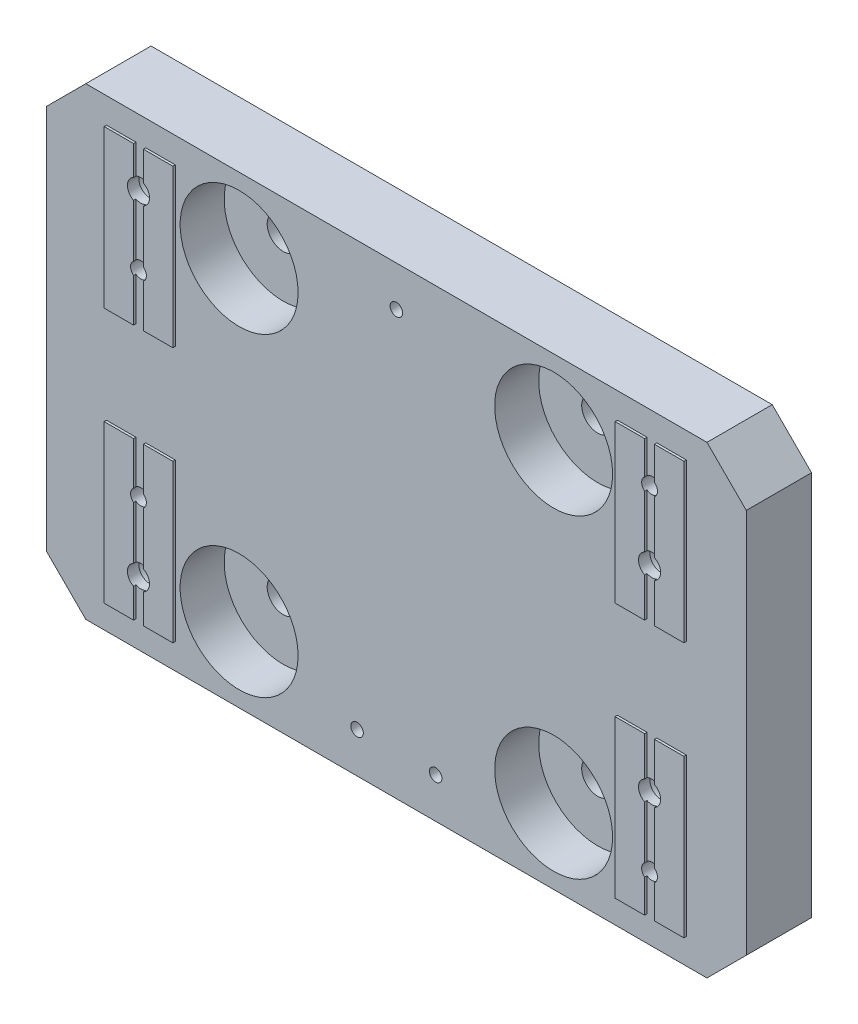
SolidWorks part; units mm, degrees
material "AISI 304"
ref_plane "Front" through (0, 0, 0) normal (0, 0, 1) x (1, 0, 0)
ref_plane "Top" through (0, 0, 0) normal (0, 1, 0) x (1, 0, 0)
ref_plane "Right" through (0, 0, 0) normal (1, 0, 0) x (0, 0, -1)
sketch "Sketch3" plane through (0, 0, 0) normal (0, 0, 1) x (1, 0, 0)
  line L1 (0, 0) -> (226.06, 0)
  line L2 (0, 0) -> (0, -149.86)
  line L3 (0, -149.86) -> (226.06, -149.86)
  line L4 (226.06, 0) -> (226.06, -149.86)
  dimension "D1" = 226.06
  dimension "D2" = 149.86
extrude "Extrude2" add sketch "Sketch3" along normal blind 21.844
sketch "Sketch4" plane through (0, 0, 21.844) normal (0, 0, 1) x (1, 0, 0)
  line L0 (0, -74.93) -> (226.06, -74.93) construction
  line L1 (0, 0) -> (0, -149.86) construction
  line L2 (226.06, -149.86) -> (226.06, 0) construction
  line L3 (113.03, 0) -> (113.03, -149.86) construction
  line L4 (226.06, 0) -> (0, 0) construction
  line L5 (0, -149.86) -> (226.06, -149.86) construction
  line L6 (41.6052, -141.605) -> (19.3802, -141.605)
  line L7 (41.6052, -8.255) -> (41.6052, -59.055)
  line L8 (19.3802, -8.255) -> (19.3802, -59.055)
  line L9 (41.6052, -90.805) -> (19.3802, -90.805)
  line L10 (41.6052, -141.605) -> (41.6052, -90.805)
  line L11 (19.3802, -141.605) -> (19.3802, -90.805)
  line L12 (41.6052, -59.055) -> (19.3802, -59.055)
  line L13 (184.4548, -141.605) -> (184.4548, -90.805)
  line L14 (206.6798, -141.605) -> (206.6798, -90.805)
  line L15 (41.6052, -8.255) -> (19.3802, -8.255)
  line L16 (184.4548, -8.255) -> (184.4548, -59.055)
  line L17 (206.6798, -8.255) -> (206.6798, -59.055)
  line L18 (206.6798, -141.605) -> (184.4548, -141.605)
  line L19 (0, 0) -> (226.06, 0)
  line L20 (0, 0) -> (0, -149.86)
  line L21 (0, -149.86) -> (226.06, -149.86)
  line L22 (226.06, 0) -> (226.06, -149.86)
  line L23 (206.6798, -90.805) -> (184.4548, -90.805)
  line L24 (206.6798, -59.055) -> (184.4548, -59.055)
  line L25 (206.6798, -8.255) -> (184.4548, -8.255)
  dimension "D5" = 15.875
  dimension "D6" = 15.875
  dimension "D7" = 50.8
  dimension "D8" = 50.8
  dimension "D9" = 71.4248
  dimension "D10" = 71.4248
  dimension "D12" = 22.225
extrude "Extrude4" cut sketch "Sketch4" against normal blind 0.762
hole_wizard "1/4-20 Tapped Hole1" positions "Sketch13" profile "Sketch12" tap size "1/4-20" standard "Ansi Inch" end condition through all
sketch "Sketch13" plane through (0, 0, 0) normal (0, 0, -1) x (-1, 0, 0)
  line L0 (-226.06, -74.93) -> (0, -74.93) construction
  line L1 (-226.06, -149.86) -> (-226.06, 0) construction
  line L2 (0, 0) -> (0, -149.86) construction
  line L4 (-113.03, 0) -> (-113.03, -149.86) construction
  line L5 (-226.06, 0) -> (0, 0) construction
  line L6 (0, -149.86) -> (-226.06, -149.86) construction
  line L11 (-195.58, -20.955) -> (-195.58, -74.93) construction
  line L13 (-195.58, -74.93) -> (-195.58, -128.905) construction
  line L15 (-30.48, -43.18) -> (-30.48, -74.93) construction
  line L17 (-30.48, -74.93) -> (-30.48, -106.68) construction
  point P3 (-195.58, -20.955)
  point P5 (-195.58, -128.905)
  point P7 (-30.48, -43.18)
  point P9 (-30.48, -106.68)
  dimension "D1" = 82.55
  dimension "D2" = 82.55
  dimension "D3" = 107.95
  dimension "D4" = 63.5
sketch "Sketch12" plane through (195.58, -20.955, 0) normal (1, 0, 0) x (0, 1, 0)
  line L0 (0, 0) -> (0, 21.844)
  line L1 (0, 21.844) -> (2.5527, 21.844)
  line L2 (2.5527, 21.844) -> (2.5527, 0)
  line L5 (2.5527, 0) -> (0, 0)
  line L11 (0, -6.35) -> (0, 107.95) construction
  dimension "Thru Tap Drill Dia." = 5.1054
  dimension "Thru Tap Drill Depth" = 21.844
cosmetic thread "Hole Thread5" parameters "D2"=6.35
cosmetic thread "Hole Thread6" parameters "D2"=6.35
cosmetic thread "Hole Thread7" parameters "D2"=6.35
cosmetic thread "Hole Thread8" parameters "D2"=6.35
hole_wizard "CBORE for 3/8 Socket Head Cap Screw1" positions "Sketch16" profile "Sketch15" counterbore size "3/8" standard "Ansi Inch" end condition through all
sketch "Sketch16" plane through (0, 0, 21.082) normal (0, 0, 1) x (1, 0, 0)
  line L0 (163.83, -125.73) -> (62.23, -125.73) construction
  line L1 (163.83, -24.13) -> (163.83, -125.73) construction
  line L2 (163.83, -24.13) -> (62.23, -24.13) construction
  line L3 (62.23, -125.73) -> (62.23, -24.13) construction
  line L4 (226.06, -74.93) -> (163.83, -74.93) construction
  line L5 (226.06, -149.86) -> (226.06, 0) construction
  line L6 (113.03, -149.86) -> (113.03, -125.73) construction
  line L7 (0, -149.86) -> (226.06, -149.86) construction
  point P0 (62.23, -125.73)
  point P1 (163.83, -24.13)
  point P4 (62.23, -24.13)
  point P7 (163.83, -125.73)
  dimension "D1" = 101.6
  dimension "D2" = 101.6
sketch "Sketch15" plane through (62.23, -125.73, 21.082) normal (1, 0, 0) x (0, -1, 0)
  line L0 (0, 0) -> (0, 21.082)
  line L1 (0, 21.082) -> (5.1587, 21.082)
  line L3 (5.1587, 21.082) -> (5.1587, 14.224)
  line L4 (5.1587, 14.224) -> (19.05, 14.224)
  line L5 (19.05, 14.224) -> (19.05, 0)
  line L7 (19.05, 0) -> (0, 0)
  line L11 (0, -6.35) -> (0, 107.95) construction
  dimension "Thru Hole Dia." = 10.3175
  dimension "Thru Hole Depth" = 21.082
  dimension "C'Bore Dia." = 38.1
  dimension "C'Bore Depth" = 14.224
sketch "Sketch17" plane through (0, 0, 21.844) normal (0, 0, 1) x (1, 0, 0)
  line L0 (195.58, -128.905) -> (195.58, -141.605) construction
  line L1 (197.1675, -141.605) -> (193.9925, -141.605)
  line L2 (197.1675, -141.605) -> (197.1675, -8.255)
  line L3 (197.1675, -8.255) -> (193.9925, -8.255)
  line L4 (193.9925, -141.605) -> (193.9925, -8.255)
  line L5 (32.0675, -141.605) -> (28.8925, -141.605)
  line L6 (32.0675, -141.605) -> (32.0675, -8.255)
  line L7 (32.0675, -8.255) -> (28.8925, -8.255)
  line L8 (28.8925, -141.605) -> (28.8925, -8.255)
  line L9 (30.48, -106.68) -> (30.48, -141.605) construction
  line L10 (184.4548, -141.605) -> (206.6798, -141.605) construction
  line L11 (206.6798, -8.255) -> (184.4548, -8.255) construction
  line L12 (19.3802, -141.605) -> (41.6052, -141.605) construction
  line L13 (41.6052, -8.255) -> (19.3802, -8.255) construction
  dimension "D1" = 3.175
extrude "Cut-Extrude1" cut sketch "Sketch17" against normal up to surface (0.762 mm away) up to face at (81.28, -125.73, 21.082)
hole_wizard "CBORE for 1/4 Socket Head Cap Screw1" positions "Sketch20" profile "Sketch19" counterbore size "1/4" standard "Ansi Inch" end condition through all
sketch "Sketch20" plane through (0, 0, 0) normal (0, 0, -1) x (-1, 0, 0)
  line L0 (-30.48, -128.905) -> (-30.48, -20.955) construction
  line L1 (-195.58, -43.18) -> (-195.58, -106.68) construction
  line L2 (-195.58, -43.18) -> (-30.48, -43.18) construction
  line L3 (-195.58, -43.18) -> (-195.58, -20.955) construction
  line L4 (-30.48, -106.68) -> (-195.58, -106.68) construction
  line L5 (-195.58, -20.955) -> (-30.48, -20.955) construction
  line L6 (-195.58, -128.905) -> (-30.48, -128.905) construction
  line L7 (-30.48, -106.68) -> (-30.48, -128.905) construction
  point P0 (-195.58, -106.68)
  point P1 (-195.58, -43.18)
  point P3 (-30.48, -20.955)
  point P5 (-30.48, -128.905)
sketch "Sketch19" plane through (195.58, -106.68, 0) normal (1, 0, 0) x (0, 1, 0)
  line L0 (0, 0) -> (0, 21.844)
  line L1 (0, 21.844) -> (3.5712, 21.844)
  line L3 (3.5712, 21.844) -> (3.5712, 18.161)
  line L4 (5.5562, 18.161) -> (3.5712, 18.161)
  line L5 (5.5562, 18.161) -> (5.5562, 0.635)
  line L6 (5.5562, 0.635) -> (6.1913, 0)
  line L7 (6.1913, 0) -> (0, 0)
  line L8 (-5.5562, 0.635) -> (-6.1913, 0) construction
  line L11 (0, -6.35) -> (0, 107.95) construction
  dimension "Thru Hole Dia." = 7.1425
  dimension "Thru Hole Depth" = 21.844
  dimension "C'Bore Dia." = 11.1125
  dimension "C'Bore Depth" = 18.161
  dimension "Near C'Sink Dia." = 12.3825
  dimension "Near C'Sink Angle" = 90
sketch "Sketch23" plane through (0, 0, 0) normal (0, 0, -1) x (-1, 0, 0)
  line L0 (-113.03, -74.93) -> (-113.03, -136.8552) construction
  line L1 (-113.03, -136.8552) -> (-113.03, -149.86) construction
  line L2 (0, -149.86) -> (-226.06, -149.86) construction
  line L3 (-113.03, -13.0048) -> (-113.03, 0) construction
  line L4 (-226.06, 0) -> (0, 0) construction
  line L16 (-113.03, -13.0048) -> (-113.03, -74.93) construction
  line L17 (-125.73, -136.8552) -> (-100.33, -136.8552) construction
  point P0 (-125.73, -136.8552)
  point P1 (-113.03, -13.0048)
  point P54 (-100.33, -136.8552)
  dimension "D2" = 25.4
  dimension "D3" = 61.9252
  dimension "D4" = 61.9252
hole_wizard "#10-32 Tapped Hole1" positions "Sketch22" profile "Sketch21" tap size "#10-32" standard "Ansi Inch" end condition through all
sketch "Sketch22" plane through (0, 0, 0) normal (0, 0, -1) x (-1, 0, 0)
  point P0 (-100.33, -136.8552)
  point P1 (-125.73, -136.8552)
  point P14 (-113.03, -13.0048)
sketch "Sketch21" plane through (100.33, -136.8552, 0) normal (1, 0, 0) x (0, 1, 0)
  line L0 (0, 0) -> (0, 21.844)
  line L1 (0, 21.844) -> (2.0193, 21.844)
  line L2 (2.0193, 21.844) -> (2.0193, 0)
  line L5 (2.0193, 0) -> (0, 0)
  line L11 (0, -6.35) -> (0, 107.95) construction
  dimension "Thru Tap Drill Dia." = 4.0386
  dimension "Thru Tap Drill Depth" = 21.844
cosmetic thread "Hole Thread9" parameters "D1"=12.7, "D2"=4.826
cosmetic thread "Hole Thread10" parameters "D1"=12.7, "D2"=4.826
cosmetic thread "Hole Thread11" parameters "D1"=12.7, "D2"=4.826
chamfer "Chamfer1" distance 12.7 angle 45 4 edges at (0, 0, 10.541) (0, -149.86, 10.541) (226.06, -149.86, 10.541) (226.06, 0, 10.541)
